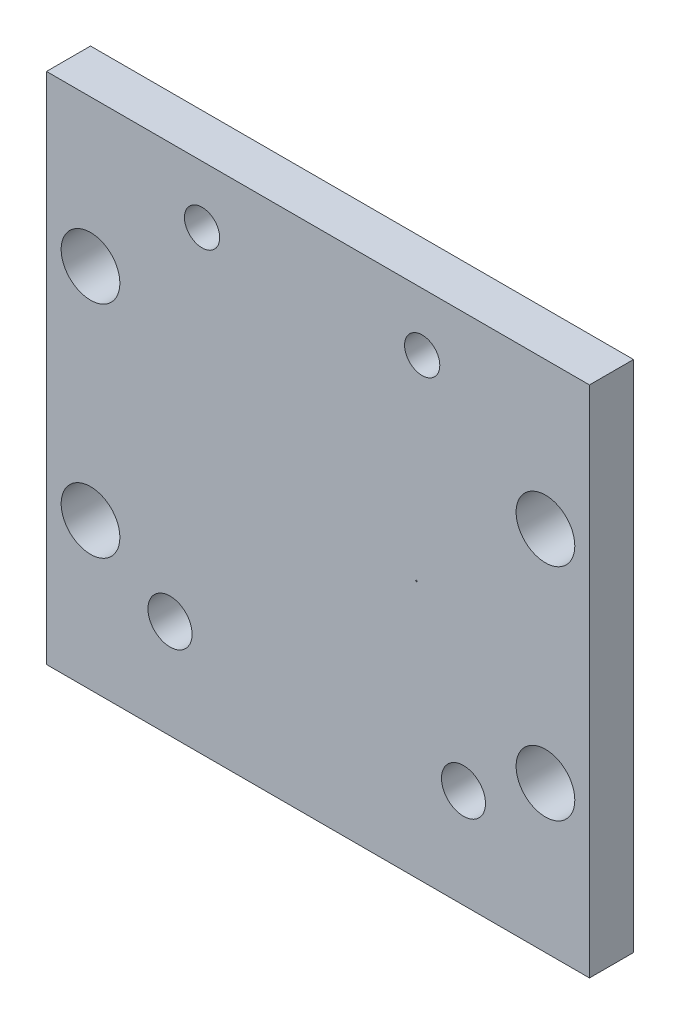
SolidWorks part; units mm, degrees
ref_plane "Front Plane" through (0, 0, 0) normal (0, 0, 1) x (1, 0, 0)
ref_plane "Top Plane" through (0, 0, 0) normal (0, 1, 0) x (1, 0, 0)
ref_plane "Right Plane" through (0, 0, 0) normal (1, 0, 0) x (0, 0, -1)
sketch "Sketch1" plane through (0, 0, 0) normal (0, 0, 1) x (1, 0, 0)
  line L0 (-7.8692, -974.9916) -> (-7.8692, 49025.0084) construction
  line L1 (-18.4694, 23.4226) -> (18.5306, 23.4226)
  line L2 (-18.4694, 23.4226) -> (-18.4694, -11.5774)
  line L3 (-18.4694, -11.5774) -> (18.5306, -11.5774)
  line L4 (18.5306, 23.4226) -> (18.5306, -11.5774)
  line L5 (7.6955, 0.4226) -> (-7.8045, 0.4226) construction
  line L6 (7.1308, -975.0265) -> (7.1308, 49024.9735) construction
  line L7 (-7.8045, -10.0774) -> (7.6955, -10.0774) construction
  line L8 (-1014.8509, -1.5774) -> (48985.1491, -1.5774) construction
  circle A0 centre (9.9455, -4.8274) radius 1.5
  circle A1 centre (6.7402, 5.9538) radius 0.0509
  circle A2 centre (-10.052, -4.8311) radius 1.5045
  circle A3 centre (-7.8692, 19.5084) radius 1.2
  circle A4 centre (7.1308, 19.4735) radius 1.2
  circle A9 centre (-15.4694, -1.5774) radius 2
  circle A10 centre (15.5306, -1.5774) radius 2
  circle A11 centre (-15.4694, 13.4226) radius 2
  circle A12 centre (15.5306, 13.4226) radius 2
  dimension "D4" = 3
  dimension "D6" = 10
  dimension "D7" = 10
  dimension "D8" = 10
  dimension "D9" = 3
  dimension "D1" = 37
  dimension "D2" = 23
  dimension "D3" = 1.5
  dimension "D5" = 3
  dimension "D10" = 3
extrude "Boss-Extrude1" add sketch "Sketch1" along normal blind 3
